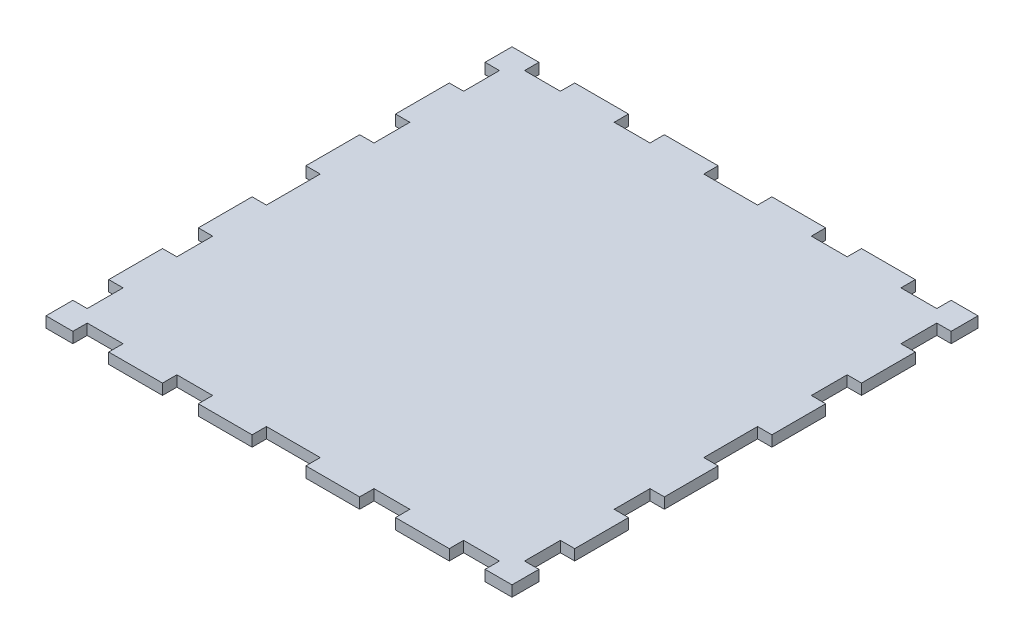
SolidWorks part; units mm, degrees
ref_plane "Front Plane" through (0, 0, 0) normal (0, 0, 1) x (1, 0, 0)
ref_plane "Top Plane" through (0, 0, 0) normal (0, 1, 0) x (1, 0, 0)
ref_plane "Right Plane" through (0, 0, 0) normal (1, 0, 0) x (0, 0, -1)
sketch "Sketch1" plane through (0, 0, 0) normal (0, 1, 0) x (1, 0, 0)
  line L0 (0, 80.1692) -> (0, -87.0923) construction
  line L3 (-65, -65) -> (-57.5, -65)
  line L5 (-65, 47.5) -> (-65, 32.5)
  line L6 (7.5, -65) -> (7.5, -61)
  line L8 (-7.5, 65) -> (-7.5, 61)
  line L9 (-7.5, 61) -> (7.5, 61)
  line L10 (7.5, 65) -> (7.5, 61)
  line L11 (-7.5, -61) -> (7.5, -61)
  line L12 (-7.5, -65) -> (-7.5, -61)
  line L13 (7.5, 65) -> (22.5, 65)
  line L14 (7.5, -65) -> (22.5, -65)
  line L16 (-32.5, 61) -> (-22.5, 61)
  line L17 (-22.5, 61) -> (-22.5, 65)
  line L18 (-32.5, 61) -> (-32.5, 65)
  line L19 (-57.5, 65) -> (-57.5, 61)
  line L20 (-57.5, 61) -> (-47.5, 61)
  line L21 (-47.5, 61) -> (-47.5, 65)
  line L22 (-47.5, 65) -> (-32.5, 65)
  line L23 (-22.5, 65) -> (-7.5, 65)
  line L24 (57.5, 65) -> (57.5, 61)
  line L25 (57.5, 61) -> (47.5, 61)
  line L26 (47.5, 61) -> (47.5, 65)
  line L27 (32.5, 61) -> (32.5, 65)
  line L28 (32.5, 61) -> (22.5, 61)
  line L29 (22.5, 61) -> (22.5, 65)
  line L30 (57.5, -65) -> (57.5, -61)
  line L31 (57.5, -61) -> (47.5, -61)
  line L32 (47.5, -61) -> (47.5, -65)
  line L33 (32.5, -61) -> (22.5, -61)
  line L34 (22.5, -61) -> (22.5, -65)
  line L35 (-22.5, -61) -> (-22.5, -65)
  line L36 (-32.5, -61) -> (-22.5, -61)
  line L37 (-32.5, -61) -> (-32.5, -65)
  line L38 (-57.5, -65) -> (-57.5, -61)
  line L39 (-47.5, -61) -> (-47.5, -65)
  line L40 (-57.5, -61) -> (-47.5, -61)
  line L41 (-22.5, -65) -> (-7.5, -65)
  line L42 (-47.5, -65) -> (-32.5, -65)
  line L43 (57.5, -65) -> (65, -65)
  line L44 (32.5, -61) -> (32.5, -65)
  line L45 (32.5, -65) -> (47.5, -65)
  line L46 (57.5, 65) -> (65, 65)
  line L47 (32.5, 65) -> (47.5, 65)
  line L48 (65, -7.5) -> (61, -7.5)
  line L49 (61, -7.5) -> (61, 7.5)
  line L50 (61, 7.5) -> (65, 7.5)
  line L51 (65, 22.5) -> (61, 22.5)
  line L52 (61, 22.5) -> (61, 32.5)
  line L53 (61, 32.5) -> (65, 32.5)
  line L54 (65, 47.5) -> (61, 47.5)
  line L55 (61, 47.5) -> (61, 57.5)
  line L56 (61, 57.5) -> (65, 57.5)
  line L57 (65, 47.5) -> (65, 32.5)
  line L58 (65, 22.5) -> (65, 7.5)
  line L60 (61, -57.5) -> (65, -57.5)
  line L61 (61, -47.5) -> (61, -57.5)
  line L62 (65, -47.5) -> (61, -47.5)
  line L63 (61, -22.5) -> (61, -32.5)
  line L64 (61, -32.5) -> (65, -32.5)
  line L65 (65, -22.5) -> (61, -22.5)
  line L68 (-61, -57.5) -> (-65, -57.5)
  line L69 (-61, -47.5) -> (-61, -57.5)
  line L70 (-65, -47.5) -> (-61, -47.5)
  line L71 (-61, -32.5) -> (-65, -32.5)
  line L72 (-61, -22.5) -> (-61, -32.5)
  line L73 (-65, -22.5) -> (-61, -22.5)
  line L74 (-65, -7.5) -> (-61, -7.5)
  line L75 (-61, -7.5) -> (-61, 7.5)
  line L76 (-61, 7.5) -> (-65, 7.5)
  line L77 (-61, 22.5) -> (-61, 32.5)
  line L78 (-65, 22.5) -> (-61, 22.5)
  line L79 (-61, 32.5) -> (-65, 32.5)
  line L80 (-65, 47.5) -> (-61, 47.5)
  line L81 (-61, 47.5) -> (-61, 57.5)
  line L82 (-61, 57.5) -> (-65, 57.5)
  line L84 (65, -7.5) -> (65, -22.5)
  line L85 (65, -32.5) -> (65, -47.5)
  line L86 (65, -57.5) -> (65, -65)
  line L89 (-65, -7.5) -> (-65, -22.5)
  line L91 (-65, 65) -> (-57.5, 65)
  line L94 (-65, 22.5) -> (-65, 7.5)
  line L95 (-65, -57.5) -> (-65, -65)
  line L96 (-65, -32.5) -> (-65, -47.5)
  line L98 (-65, 57.5) -> (-65, 65)
  line L99 (65, 65) -> (65, 57.5)
  dimension "D3" = 15
  dimension "D4" = 10
  dimension "D5" = 15
  dimension "D6" = 7.5
  dimension "D7" = 4
  dimension "D8" = 15
  dimension "D9" = 10
  dimension "D10" = 15
  dimension "D11" = 10
  dimension "D12" = 10
  dimension "D13" = 10
  dimension "D14" = 15
  dimension "D15" = 10
  dimension "D16" = 4
  dimension "D17" = 15
  dimension "D18" = 15
  dimension "D19" = 4
  dimension "D20" = 15
  dimension "D21" = 10
  dimension "D22" = 10
  dimension "D23" = 4
  dimension "D24" = 4
  dimension "D25" = 15
  dimension "D26" = 15
  dimension "D27" = 15
  dimension "D28" = 15
  dimension "D29" = 10
  dimension "D30" = 10
extrude "Boss-Extrude1" add sketch "Sketch1" along normal blind 3
